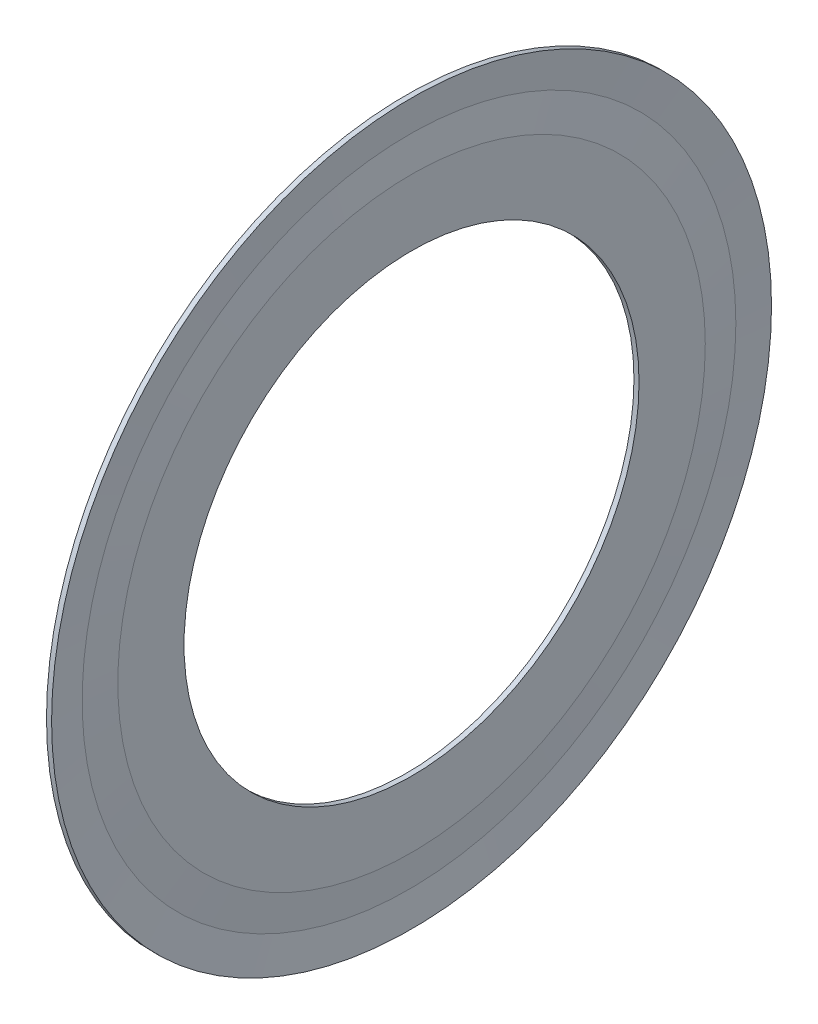
SolidWorks part; units mm, degrees
ref_plane "Front Plane" through (0, 0, 0) normal (0, 0, 1) x (1, 0, 0)
ref_plane "Top Plane" through (0, 0, 0) normal (0, 1, 0) x (1, 0, 0)
ref_plane "Right Plane" through (0, 0, 0) normal (1, 0, 0) x (0, 0, -1)
ref_plane "Plane1" through (0, 0, 0) normal (0, 0, 1) x (1, 0, 0)
sketch "Sketch1" plane through (0, 0, 0) normal (0, 0, 1) x (1, 0, 0)
  line L0 (13.116, 11.3296) -> (13.116, 10.2)
  line L1 (13.116, 10.2) -> (13.293, 7.9)
  line L2 (13.293, 7.9) -> (13.47, 7.9)
  line L3 (13.47, 7.9) -> (13.47, 10.2)
  line L4 (13.47, 10.2) -> (13.3815, 11.35)
  line L5 (13.3815, 11.35) -> (13.47, 12.5)
  line L6 (13.47, 12.5) -> (13.293, 12.5)
  line L7 (13.293, 12.5) -> (13.116, 11.3296)
  line L8 (50, 0) -> (-50, 0) construction
revolve "Revolve1" add sketch "Sketch1" angle 360 about L8
